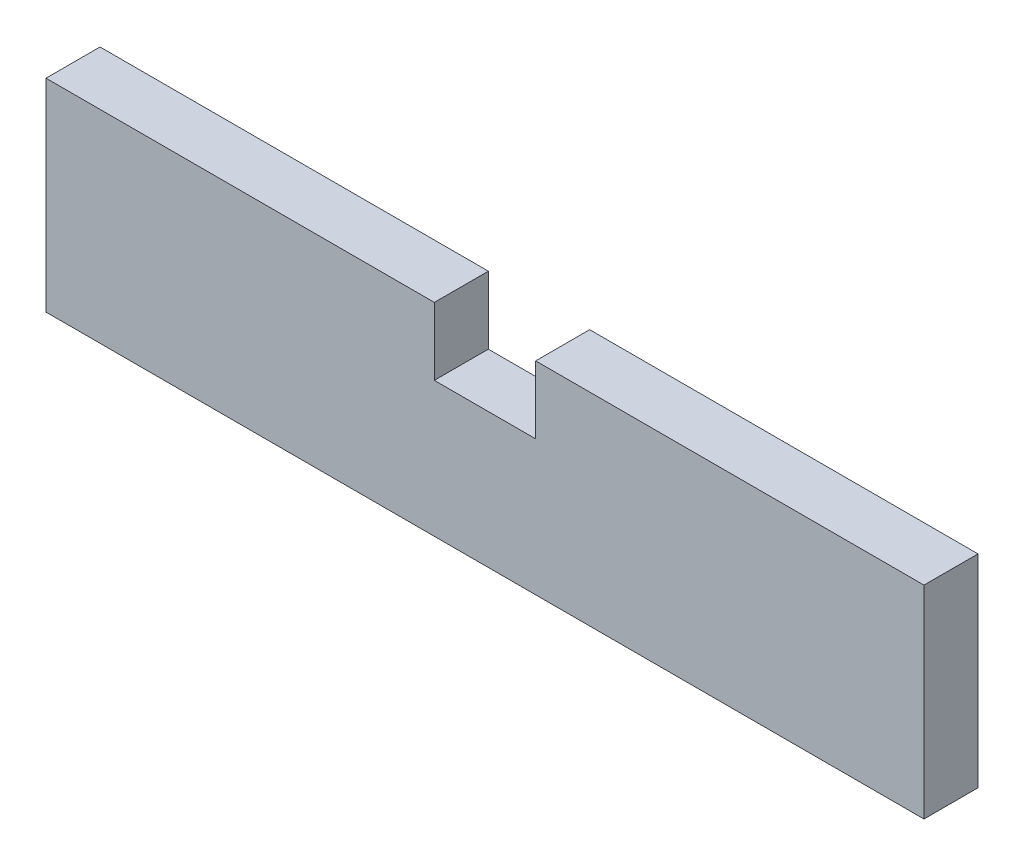
SolidWorks part; units mm, degrees
ref_plane "Ebene vorne" through (0, 0, 0) normal (0, 0, 1) x (1, 0, 0)
ref_plane "Ebene oben" through (0, 0, 0) normal (0, 1, 0) x (1, 0, 0)
ref_plane "Ebene rechts" through (0, 0, 0) normal (1, 0, 0) x (0, 0, -1)
sketch "Skizze1" plane through (0, 0, 0) normal (0, 0, 1) x (1, 0, 0)
  line L1 (0, 0) -> (65, 0)
  line L2 (0, 0) -> (0, 15)
  line L3 (0, 15) -> (65, 15)
  line L4 (65, 0) -> (65, 15)
  dimension "D1" = 15
  dimension "D2" = 65
extrude "Aufsatz-Linear austragen1" add sketch "Skizze1" along normal blind 4
sketch "Skizze2" plane through (0, 0, 4) normal (0, 0, 1) x (1, 0, 0)
  line L5 (32.5, 23.0473) -> (32.5, -13.4742) construction
  line L6 (65, 15) -> (0, 15) construction
  line L9 (28.75, 15) -> (36.25, 15)
  line L10 (28.75, 15) -> (28.75, 10)
  line L11 (28.75, 10) -> (36.25, 10)
  line L12 (36.25, 15) -> (36.25, 10)
  point P4 (32.5, 15)
  point P9 (32.5, 10)
  dimension "D1" = 7.5
  dimension "D2" = 5
extrude "Schnitt-Linear austragen1" cut sketch "Skizze2" against normal up to next
